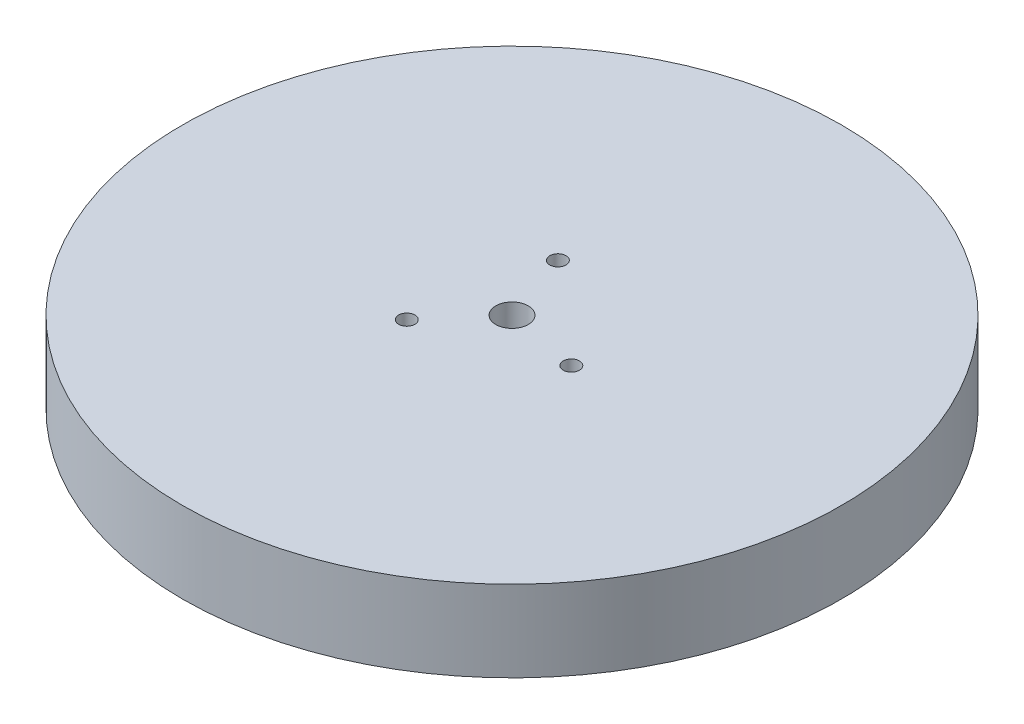
SolidWorks part; units mm, degrees
ref_plane "Front Plane" through (0, 0, 0) normal (0, 0, 1) x (1, 0, 0)
ref_plane "Top Plane" through (0, 0, 0) normal (0, 1, 0) x (1, 0, 0)
ref_plane "Right Plane" through (0, 0, 0) normal (1, 0, 0) x (0, 0, -1)
sketch "Sketch1" plane through (0, 0, 0) normal (0, 1, 0) x (1, 0, 0)
  circle A0 centre (0, 0) radius 101.6
  circle A1 centre (0, 0) radius 5
  dimension "D1" = 10
  dimension "D2" = 203.2
extrude "Boss-Extrude8" add sketch "Sketch1" along normal blind 25 contours A0 | A1
sketch "Sketch2" plane through (0, 0, 0) normal (0, -1, 0) x (1, 0, 0)
  circle A0 centre (22.5931, 4.3073) radius 2.5
  circle A1 centre (-7.5663, -21.7198) radius 2.5
  circle A2 centre (-15.0268, 17.4125) radius 2.5
  dimension "D1" = 5
  dimension "D4" = 39.8372
  dimension "D9" = 39.8372
  dimension "D10" = 39.8372
extrude "Cut-Extrude1" cut sketch "Sketch2" against normal through all
